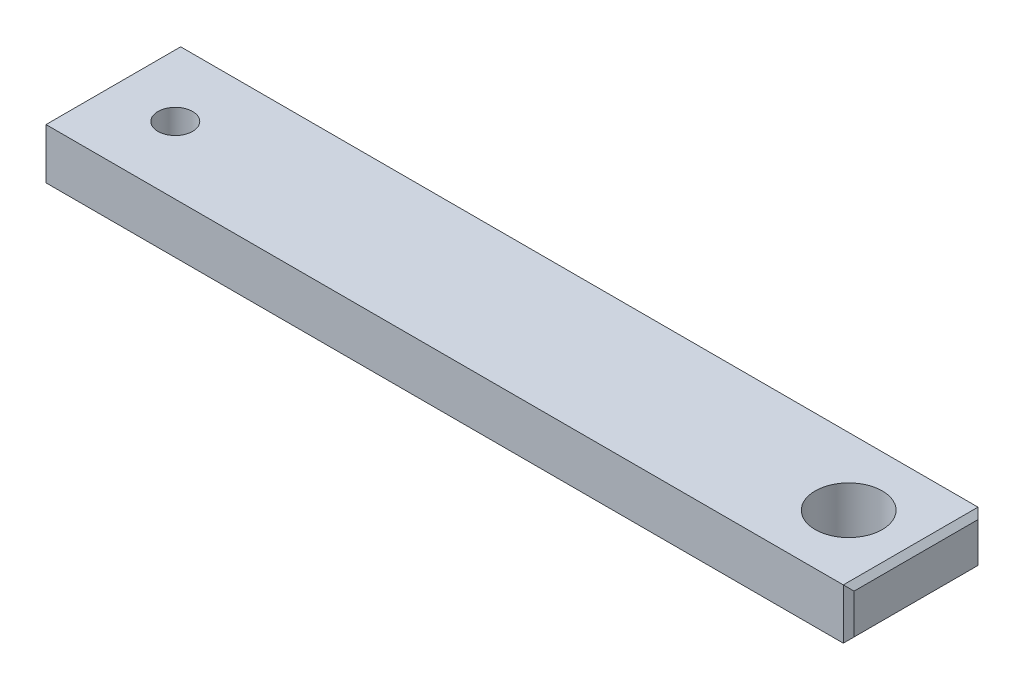
SolidWorks part; units mm, degrees
material "6061-T6 (SS)"
ref_plane "Front Plane" through (0, 0, 0) normal (0, 0, 1) x (1, 0, 0)
ref_plane "Top Plane" through (0, 0, 0) normal (0, 1, 0) x (1, 0, 0)
ref_plane "Right Plane" through (0, 0, 0) normal (1, 0, 0) x (0, 0, -1)
sketch "Sketch1" plane through (0, 0, 0) normal (0, 1, 0) x (1, 0, 0)
  line L0 (-63.5, 0) -> (0, 0) construction
  line L1 (-63.5, 6.35) -> (0, 6.35)
  line L2 (-63.5, -6.35) -> (0, -6.35)
  line L4 (-69.85, 6.35) -> (6.35, 6.35)
  line L5 (-69.85, 6.35) -> (-69.85, -6.35)
  line L6 (-69.85, -6.35) -> (6.35, -6.35)
  line L7 (6.35, 6.35) -> (6.35, -6.35)
  arc A0 (-63.5, 6.35) -> (-63.5, -6.35) centre (-63.5, 0) ccw
  arc A1 (0, -6.35) -> (0, 6.35) centre (0, 0) ccw
  point P2 (-31.75, 0)
  point P9 (-69.85, 0)
  point P10 (6.35, 0)
  dimension "D2" = 76.2
  dimension "D1" = 12.7
extrude "Boss-Extrude2" add sketch "Sketch1" along normal blind 4.7625
sketch "Sketch2" plane through (0, 4.7625, 0) normal (0, 1, 0) x (1, 0, 0)
  line L0 (6.35, 6.35) -> (6.35, -6.35) construction
  line L5 (0, 6.35) -> (0, -6.35)
  line L6 (-69.85, -6.35) -> (6.35, -6.35) construction
  line L7 (-69.85, 6.35) -> (6.35, 6.35) construction
  circle A0 centre (0, 0) radius 3.1623
  dimension "D1" = 6.3246
  dimension "D2" = 6.35
hole_wizard "#4 Clearance Hole1" positions "Sketch3" profile "Sketch4" hole size "#4" standard "ANSI Inch" end condition through all
sketch "Sketch3" plane through (0, 4.7625, 0) normal (0, 1, 0) x (1, 0, 0)
  line L0 (-63.5, 6.35) -> (-63.5, -6.35)
  line L1 (-69.85, 6.35) -> (6.35, 6.35) construction
  line L2 (-69.85, -6.35) -> (6.35, -6.35) construction
  line L4 (-69.85, 6.35) -> (-69.85, -6.35) construction
  point P0 (-63.5, 0)
  dimension "D1" = 6.35
sketch "Sketch4" plane through (-63.5, 4.7625, 0) normal (1, 0, 0) x (0, 0, 1)
  line L0 (0, 0) -> (0, 4.7625)
  line L1 (0, 4.7625) -> (1.6319, 4.7625)
  line L2 (1.6319, 4.7625) -> (1.6319, 0)
  line L5 (1.6319, 0) -> (0, 0)
  line L11 (0, -6.35) -> (0, 107.95) construction
  dimension "Thru Hole Dia." = 3.2639
  dimension "Thru Hole Depth" = 4.7625
extrude "Cut-Extrude1" cut sketch "Sketch2" against normal through all contours L5 A0 | L5 A0
chamfer "Chamfer1" distance 0.508 angle 45 8 edges at (-69.85, 2.3813, -6.35) (-69.85, 0, 0) (-69.85, 4.7625, 0) (-69.85, 2.3813, 6.35) (6.35, 2.3813, 6.35) (6.35, 0, 0) (6.35, 4.7625, 0) (6.35, 2.3813, -6.35)
